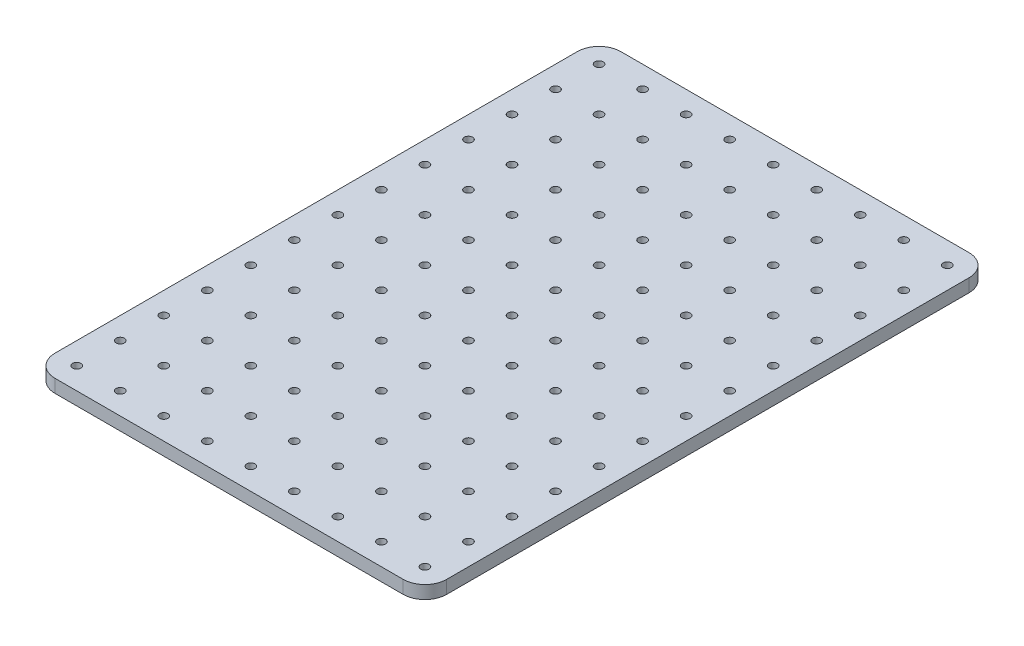
SolidWorks part; units mm, degrees
ref_plane "Front" through (0, 0, 0) normal (0, 0, 1) x (1, 0, 0)
ref_plane "Top" through (0, 0, 0) normal (0, 1, 0) x (1, 0, 0)
ref_plane "Right" through (0, 0, 0) normal (1, 0, 0) x (0, 0, -1)
sketch "Sketch1" plane through (0, 0, 0) normal (0, 1, 0) x (1, 0, 0)
  line L1 (-45, -65) -> (45, -65)
  line L2 (-45, -65) -> (-45, 65)
  line L3 (-45, 65) -> (45, 65)
  line L4 (45, -65) -> (45, 65)
  line L5 (-45, -65) -> (45, 65) construction
  line L6 (-45, 65) -> (45, -65) construction
  point P0 (0, 0)
  dimension "D1" = 90
  dimension "D2" = 130
extrude "Boss-Extrude1" add sketch "Sketch1" along normal blind 3
sketch "Sketch2" plane through (0, 3, 0) normal (0, 1, 0) x (1, 0, 0)
  line L0 (-40, 60) -> (-45, 60) construction
  line L1 (-45, 65) -> (-45, -65) construction
  line L2 (-40, 60) -> (-30, 60) construction
  line L3 (-40, 60) -> (-40, 50) construction
  line L4 (-40, 60) -> (-40, 65) construction
  line L5 (45, 65) -> (-45, 65) construction
  circle A0 centre (-40, 60) radius 0.95
  circle A1 centre (-30, 60) radius 0.95
  circle A2 centre (-20, 60) radius 0.95
  circle A3 centre (-10, 60) radius 0.95
  circle A4 centre (0, 60) radius 0.95
  circle A5 centre (10, 60) radius 0.95
  circle A6 centre (20, 60) radius 0.95
  circle A7 centre (-40, -40) radius 0.95
  circle A8 centre (-40, -20) radius 0.95
  circle A9 centre (-30, -20) radius 0.95
  circle A10 centre (-30, 50) radius 0.95
  circle A11 centre (-20, 50) radius 0.95
  circle A12 centre (-10, 50) radius 0.95
  circle A13 centre (0, 50) radius 0.95
  circle A14 centre (10, 50) radius 0.95
  circle A15 centre (20, 50) radius 0.95
  circle A16 centre (-30, -40) radius 0.95
  circle A17 centre (-20, -20) radius 0.95
  circle A18 centre (-10, -20) radius 0.95
  circle A19 centre (-30, 40) radius 0.95
  circle A20 centre (-20, 40) radius 0.95
  circle A21 centre (-10, 40) radius 0.95
  circle A22 centre (0, 40) radius 0.95
  circle A23 centre (10, 40) radius 0.95
  circle A24 centre (20, 40) radius 0.95
  circle A25 centre (-20, -40) radius 0.95
  circle A26 centre (0, -20) radius 0.95
  circle A27 centre (10, -20) radius 0.95
  circle A28 centre (-30, 30) radius 0.95
  circle A29 centre (-20, 30) radius 0.95
  circle A30 centre (-10, 30) radius 0.95
  circle A31 centre (0, 30) radius 0.95
  circle A32 centre (10, 30) radius 0.95
  circle A33 centre (20, 30) radius 0.95
  circle A34 centre (-10, -40) radius 0.95
  circle A35 centre (20, -20) radius 0.95
  circle A36 centre (0, -40) radius 0.95
  circle A37 centre (-40, 50) radius 0.95
  circle A38 centre (-40, 40) radius 0.95
  circle A39 centre (-40, 30) radius 0.95
  circle A40 centre (-40, 20) radius 0.95
  circle A41 centre (-30, 20) radius 0.95
  circle A42 centre (-20, 20) radius 0.95
  circle A43 centre (-10, 20) radius 0.95
  circle A44 centre (0, 20) radius 0.95
  circle A45 centre (10, 20) radius 0.95
  circle A46 centre (20, 20) radius 0.95
  circle A47 centre (10, -40) radius 0.95
  circle A48 centre (-40, -30) radius 0.95
  circle A49 centre (-30, -30) radius 0.95
  circle A50 centre (-20, -30) radius 0.95
  circle A51 centre (-10, -30) radius 0.95
  circle A52 centre (0, -30) radius 0.95
  circle A53 centre (10, -30) radius 0.95
  circle A54 centre (20, -30) radius 0.95
  circle A55 centre (20, -40) radius 0.95
  circle A56 centre (-40, -50) radius 0.95
  circle A57 centre (-30, -50) radius 0.95
  circle A58 centre (-20, -50) radius 0.95
  circle A59 centre (-10, -50) radius 0.95
  circle A60 centre (0, -50) radius 0.95
  circle A61 centre (10, -50) radius 0.95
  circle A62 centre (20, -50) radius 0.95
  circle A63 centre (-40, -60) radius 0.95
  circle A64 centre (-30, -60) radius 0.95
  circle A65 centre (-20, -60) radius 0.95
  circle A66 centre (-10, -60) radius 0.95
  circle A67 centre (0, -60) radius 0.95
  circle A68 centre (10, -60) radius 0.95
  circle A69 centre (20, -60) radius 0.95
  circle A70 centre (30, 60) radius 0.95
  circle A71 centre (30, 50) radius 0.95
  circle A72 centre (30, 40) radius 0.95
  circle A73 centre (30, 30) radius 0.95
  circle A74 centre (30, 20) radius 0.95
  circle A75 centre (30, 10) radius 0.95
  circle A76 centre (30, 0) radius 0.95
  circle A77 centre (30, -10) radius 0.95
  circle A78 centre (30, -20) radius 0.95
  circle A79 centre (30, -30) radius 0.95
  circle A80 centre (30, -40) radius 0.95
  circle A81 centre (30, -50) radius 0.95
  circle A82 centre (30, -60) radius 0.95
  circle A83 centre (40, 60) radius 0.95
  circle A84 centre (40, 50) radius 0.95
  circle A85 centre (40, 40) radius 0.95
  circle A86 centre (-40, 10) radius 0.95
  circle A87 centre (-30, 10) radius 0.95
  circle A88 centre (-20, 10) radius 0.95
  circle A89 centre (-10, 10) radius 0.95
  circle A90 centre (0, 10) radius 0.95
  circle A91 centre (40, 30) radius 0.95
  circle A92 centre (40, 20) radius 0.95
  circle A93 centre (40, 10) radius 0.95
  circle A94 centre (40, 0) radius 0.95
  circle A95 centre (10, 10) radius 0.95
  circle A96 centre (20, 10) radius 0.95
  circle A97 centre (40, -10) radius 0.95
  circle A98 centre (40, -20) radius 0.95
  circle A99 centre (40, -30) radius 0.95
  circle A100 centre (40, -40) radius 0.95
  circle A101 centre (40, -50) radius 0.95
  circle A102 centre (40, -60) radius 0.95
  circle A103 centre (-40, -70) radius 0.95
  circle A104 centre (-30, -70) radius 0.95
  circle A105 centre (-20, -70) radius 0.95
  circle A106 centre (-10, -70) radius 0.95
  circle A107 centre (0, -70) radius 0.95
  circle A108 centre (-40, 0) radius 0.95
  circle A109 centre (-30, 0) radius 0.95
  circle A110 centre (-20, 0) radius 0.95
  circle A111 centre (-10, 0) radius 0.95
  circle A112 centre (0, 0) radius 0.95
  circle A113 centre (10, 0) radius 0.95
  circle A114 centre (20, 0) radius 0.95
  circle A115 centre (10, -70) radius 0.95
  circle A116 centre (20, -70) radius 0.95
  circle A117 centre (30, -70) radius 0.95
  circle A118 centre (40, -70) radius 0.95
  circle A119 centre (-40, -80) radius 0.95
  circle A120 centre (-30, -80) radius 0.95
  circle A121 centre (-20, -80) radius 0.95
  circle A122 centre (-10, -80) radius 0.95
  circle A123 centre (0, -80) radius 0.95
  circle A124 centre (10, -80) radius 0.95
  circle A125 centre (20, -80) radius 0.95
  circle A126 centre (-40, -10) radius 0.95
  circle A127 centre (-30, -10) radius 0.95
  circle A128 centre (-20, -10) radius 0.95
  circle A129 centre (-10, -10) radius 0.95
  circle A130 centre (0, -10) radius 0.95
  circle A131 centre (10, -10) radius 0.95
  circle A132 centre (20, -10) radius 0.95
  circle A133 centre (30, -80) radius 0.95
  circle A134 centre (40, -80) radius 0.95
  circle A135 centre (-40, -90) radius 0.95
  circle A136 centre (-30, -90) radius 0.95
  circle A137 centre (-20, -90) radius 0.95
  circle A138 centre (-10, -90) radius 0.95
  circle A139 centre (0, -90) radius 0.95
  circle A140 centre (10, -90) radius 0.95
  circle A141 centre (20, -90) radius 0.95
  circle A142 centre (30, -90) radius 0.95
  circle A143 centre (40, -90) radius 0.95
  circle A144 centre (-40, -100) radius 0.95
  circle A145 centre (-30, -100) radius 0.95
  circle A146 centre (-20, -100) radius 0.95
  circle A147 centre (-10, -100) radius 0.95
  circle A148 centre (0, -100) radius 0.95
  circle A149 centre (10, -100) radius 0.95
  circle A150 centre (20, -100) radius 0.95
  circle A151 centre (30, -100) radius 0.95
  circle A152 centre (40, -100) radius 0.95
  circle A153 centre (-40, -110) radius 0.95
  circle A154 centre (-30, -110) radius 0.95
  circle A155 centre (-20, -110) radius 0.95
  circle A156 centre (-10, -110) radius 0.95
  circle A157 centre (0, -110) radius 0.95
  circle A158 centre (10, -110) radius 0.95
  circle A159 centre (20, -110) radius 0.95
  circle A160 centre (30, -110) radius 0.95
  circle A161 centre (40, -110) radius 0.95
  circle A162 centre (-40, -120) radius 0.95
  circle A163 centre (-30, -120) radius 0.95
  circle A164 centre (-20, -120) radius 0.95
  circle A165 centre (-10, -120) radius 0.95
  circle A166 centre (0, -120) radius 0.95
  circle A167 centre (10, -120) radius 0.95
  circle A168 centre (20, -120) radius 0.95
  circle A169 centre (30, -120) radius 0.95
  circle A170 centre (40, -120) radius 0.95
  circle A171 centre (-40, -130) radius 0.95
  circle A172 centre (-30, -130) radius 0.95
  circle A173 centre (-20, -130) radius 0.95
  circle A174 centre (-10, -130) radius 0.95
  circle A175 centre (0, -130) radius 0.95
  circle A176 centre (10, -130) radius 0.95
  circle A177 centre (20, -130) radius 0.95
  circle A178 centre (30, -130) radius 0.95
  circle A179 centre (40, -130) radius 0.95
  dimension "D3" = 1.9
  dimension "D4" = 10
  dimension "D5" = 10
  dimension "D6" = 5
  dimension "D7" = 5
  dimension "D1" = 9
  dimension "D2" = 20
extrude "Cut-Extrude1" cut sketch "Sketch2" against normal through all
fillet "Fillet1" radius 5 4 edges at (45, 1.5, 65) (-45, 1.5, 65) (-45, 1.5, -65) (45, 1.5, -65)
